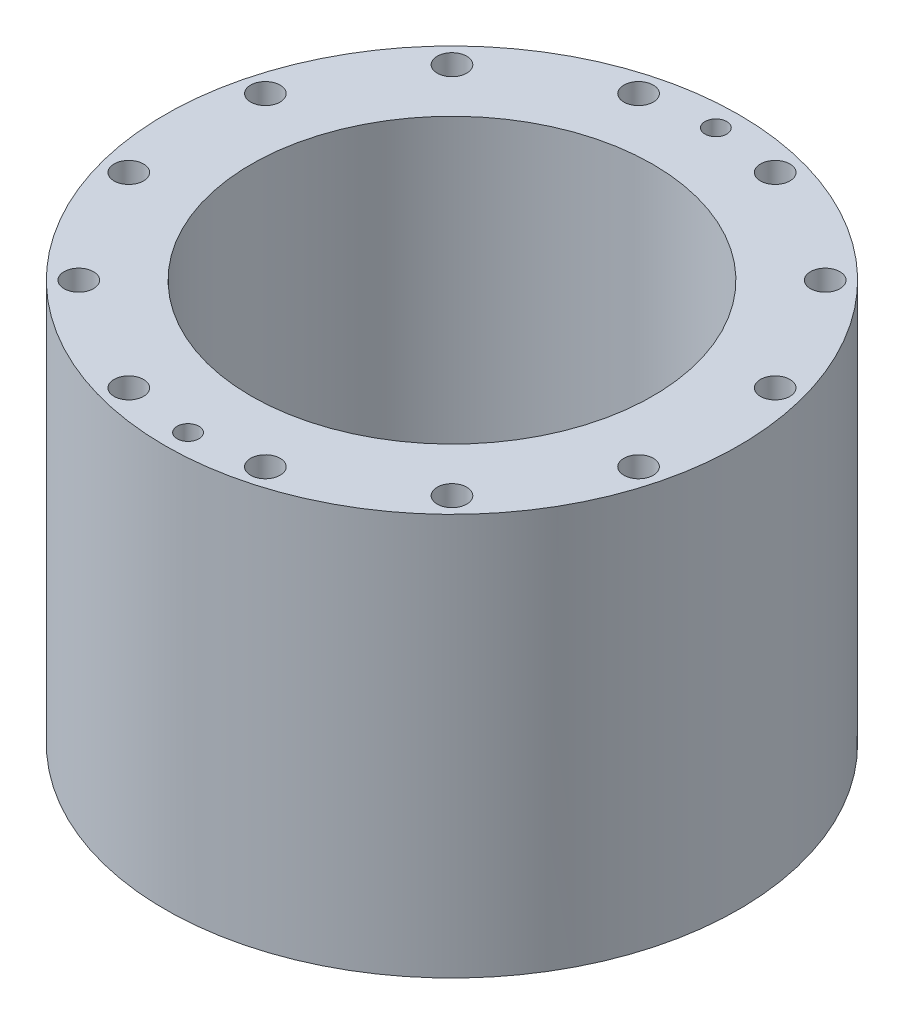
SolidWorks part; units mm, degrees
other "Markup1" [suppressed]
sketch "Sketch50" [suppressed] plane through (-56.3562, 381, -56.3562) normal (-0.5994, 0.5147, -0.613) x (-0.7086, 0.0149, 0.7054)
material "6061 Alloy"
ref_plane "Front Plane" through (0, 0, 0) normal (0, 0, 1) x (1, 0, 0)
ref_plane "Top Plane" through (0, 0, 0) normal (0, 1, 0) x (1, 0, 0)
ref_plane "Right Plane" through (0, 0, 0) normal (1, 0, 0) x (0, 0, -1)
sketch "Sketch2" plane through (0, 0, 0) normal (0, 1, 0) x (1, 0, 0)
  circle A0 centre (0, 0) radius 44.45
  circle A1 centre (0, 0) radius 55.88
  dimension "D1" = 111.76
  dimension "D2" = 88.9
extrude "Base Cylinder" add sketch "Sketch2" along normal blind 88.9
sketch "Sketch3" plane through (0, 0, 0) normal (0, -1, 0) x (1, 0, 0)
  circle A0 centre (0, 0) radius 44.45
  circle A1 centre (0, 0) radius 63.5
  dimension "D1" = 127
  dimension "D2" = 88.9
extrude "Aft Flange" add sketch "Sketch3" against normal up to surface (88.9 mm away) up to face at (0, 88.9, 55.88)
sketch "Sketch6" plane through (0, 0, 0) normal (0, -1, 0) x (1, 0, 0)
  circle A0 centre (0, 0) radius 50.9524
  circle A1 centre (0, 0) radius 47.4218
  dimension "D1" = 101.9048
  dimension "D2" = 94.8436
extrude "Aft O-Ring" cut sketch "Sketch6" against normal blind 1.9812
sketch "Sketch33" plane through (0, 88.9, 0) normal (0, 1, 0) x (1, 0, 0)
  circle A0 centre (0, 0) radius 48.26
  circle A1 centre (0, 0) radius 49.53
  dimension "D1" = 96.52
  dimension "3.9" = 99.06
sketch "Sketch For Bolt Holes" plane through (0, 0, 0) normal (0, -1, 0) x (1, 0, 0)
  line L0 (0, 0) -> (0, 61.86) construction
  line L1 (15.1202, 56.4294) -> (0, 0) construction
  line L2 (-15.1202, 56.4294) -> (0, 0) construction
  line L3 (41.3092, 41.3092) -> (0, 0) construction
  line L4 (0, 0) -> (56.4294, 15.1202) construction
  line L5 (56.4294, 15.1202) -> (0, 0) construction
  line L6 (0, 0) -> (56.4294, -15.1202) construction
  circle A14 centre (15.1202, 56.4294) radius 3.2639
  circle A15 centre (41.3092, 41.3092) radius 3.2639
  circle A16 centre (56.4294, 15.1202) radius 3.2639
  circle A17 centre (56.4294, -15.1202) radius 3.2639
  circle A18 centre (41.3092, -41.3092) radius 3.2639
  circle A19 centre (15.1202, -56.4294) radius 3.2639
  circle A20 centre (-15.1202, -56.4294) radius 3.2639
  circle A21 centre (-41.3092, -41.3092) radius 3.2639
  circle A22 centre (-56.4294, -15.1202) radius 3.2639
  circle A23 centre (-56.4294, 15.1202) radius 3.2639
  circle A24 centre (-41.3092, 41.3092) radius 3.2639
  circle A25 centre (-15.1202, 56.4294) radius 3.2639
  point P29 (0, 0)
  point P36 (0, 0)
  dimension "D2" = 58.42
  dimension "D1" = 6.5278
  dimension "D4" = 12
  dimension "D3" = 15
  dimension "D5" = 15
  dimension "D6" = 30
ref_plane "Hoop Mid-Plane" through (0, 190.5, 0) normal (0, 1, 0) x (1, 0, 0)
ref_plane "PressureTapHolePlane" through (0, 0, 63.5) normal (0, 0, 1) x (1, 0, 0)
ref_plane "TemperatureTapPlane" through (0, 0, -63.5) normal (0, 0, 1) x (1, 0, 0)
sketch "ThermoHole" plane through (0, 0, -63.5) normal (0, 0, 1) x (1, 0, 0)
  line L0 (-63.5, 0) -> (63.5, 0) construction
  circle A0 centre (0, 82.55) radius 3.175
  dimension "D1" = 82.55
  dimension "D2" = 6.35
hole_wizard "1/8 NPT Tapped ThermocoupleHole" [suppressed] positions "Sketch43" profile "Sketch44" size "1/8" standard "ANSI Inch"
sketch "Sketch43" plane through (0, 0, -63.5) normal (0, 0, 1) x (1, 0, 0)
  line L0 (-63.5, 0) -> (63.5, 0) construction
  point P0 (0, 82.55)
  dimension "D1" = 82.55
cosmetic thread "Hole Thread5" [suppressed] parameters "D1"=14.478, "D2"=10.739
sketch "Sketch44" plane through (0, 82.55, -63.5) normal (1, 0, 0) x (0, 1, 0)
  line L0 (0, 0) -> (0, 21.5825)
  line L1 (4.2164, 19.049) -> (0, 21.5825)
  line L2 (-4.2164, 19.049) -> (0, 21.5825) construction
  line L3 (4.2164, 19.049) -> (4.2164, 14.478)
  line L4 (4.2164, 14.478) -> (4.5374, 14.478)
  line L5 (4.5374, 14.478) -> (4.9709, 0)
  line L6 (-4.5374, 14.478) -> (-4.9709, 0) construction
  line L7 (4.9709, 0) -> (0, 0)
  line L8 (0, -6.35) -> (0, 107.95) construction
  line L11 (-4.2164, 14.478) -> (-4.5374, 14.478) construction
  dimension "Tap Drill Dia." = 8.4328
  dimension "Tap Drill Depth" = 19.049
  dimension "Thread Dia." = 9.9418
  dimension "Thread Angle" = 3.43
  dimension "Thread Depth" = 14.478
  dimension "Drill Angle" = 118
hole_wizard "3/8-24 Tapped Hole1" [suppressed] positions "Sketch48" profile "Sketch49" tap size "3/8-24" standard "ANSI Inch"
sketch "Sketch48" plane through (0, 0, 63.5) normal (0, 0, 1) x (1, 0, 0)
  line L0 (-63.5, 0) -> (63.5, 0) construction
  point P0 (0, 82.55)
  dimension "D1" = 82.55
cosmetic thread "Hole Thread4" [suppressed] parameters "D1"=3.302, "D2"=9.525
sketch "Sketch49" plane through (0, 82.55, 63.5) normal (1, 0, 0) x (0, -1, 0)
  line L0 (0, 0) -> (0, 21.5825)
  line L1 (0, 21.5825) -> (4.2164, 19.049)
  line L2 (4.2164, 19.049) -> (4.2164, 0)
  line L5 (4.2164, 0) -> (0, 0)
  line L10 (0, 21.5825) -> (-4.2164, 19.049) construction
  line L11 (0, -6.35) -> (0, 107.95) construction
  dimension "Tap Drill Dia." = 8.4328
  dimension "Tap Drill Depth" = 19.049
  dimension "Drill Angle" = 118
extrude "Cut-Extrude1" cut sketch "Sketch For Bolt Holes" against normal through all
sketch "Sketch51" plane through (0, 88.9, 0) normal (0, 1, 0) x (1, 0, 0)
  line L0 (15.1202, 56.4294) -> (-15.1202, 56.4294) construction
  line L1 (-15.1202, -56.4294) -> (15.1202, -56.4294) construction
  line L2 (0, -72.41) -> (0, 74.4694) construction
  circle A0 centre (0, 0) radius 58.42 construction
  circle A1 centre (0, 58.42) radius 2.413
  circle A2 centre (0, -58.42) radius 2.413
  dimension "D1" = 4.826
extrude "Cut-Extrude2" cut sketch "Sketch51" against normal blind 4.826
